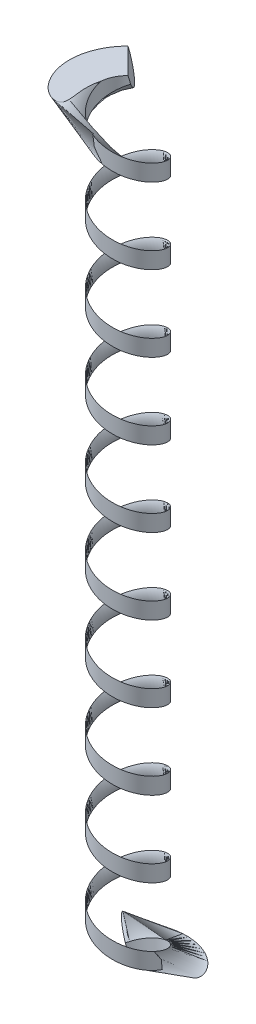
SolidWorks part; units mm, degrees
ref_plane "Front" through (0, 0, 0) normal (0, 0, 1) x (1, 0, 0)
ref_plane "Top" through (0, 0, 0) normal (0, 1, 0) x (1, 0, 0)
ref_plane "Right" through (0, 0, 0) normal (1, 0, 0) x (0, 0, -1)
sketch "Sketch1" plane through (0, 0, 0) normal (0, 1, 0) x (1, 0, 0)
  circle A0 centre (0, 0) radius 3.175
  point P4 (0, 0)
  dimension "D1" = 6.35
curve "Helix/Spiral1" pitch 5.08 height 50.8 turns 10
sweep "Sweep1" add path "Helix/Spiral1" circular profile diameter 2.54 parameters "D3"=2.54
sketch "Sketch10" plane through (0, 0, 0) normal (1, 0, 0) x (0, 0, -1)
  line L5 (-5.7814, 56.4483) -> (10.2716, 56.4483)
  line L6 (-5.7814, 56.4483) -> (-5.7814, 50.8)
  line L7 (-5.7814, 50.8) -> (10.2716, 50.8)
  line L8 (10.2716, 56.4483) -> (10.2716, 50.8)
  line L9 (-7.3012, 0) -> (8.8113, 0)
  line L10 (-7.3012, 0) -> (-7.3012, -4.697)
  line L11 (-7.3012, -4.697) -> (8.8113, -4.697)
  line L12 (8.8113, 0) -> (8.8113, -4.697)
  spline S0 degree 3 poles (2.2451, 0) (2.5372, 0.1052) (3.0105, 0.3178) (3.2574, 0.6349) (3.0097, 0.9525) (2.3035, 1.27) (1.2467, 1.5875) (0, 1.905) (-1.2467, 2.2225) (-2.3035, 2.54) (-3.0097, 2.8575) (-3.2577, 3.175) (-3.0097, 3.4925) (-2.3035, 3.81) (-0.8944, 4.2333) (0.8944, 4.6567) (2.3035, 5.08) (3.0097, 5.3975) (3.2577, 5.715) (3.0097, 6.0325) (2.3035, 6.35) (0.8944, 6.7733) (-0.8944, 7.1967) (-2.3035, 7.62) (-3.0097, 7.9375) (-3.2577, 8.255) (-3.0097, 8.5725) (-2.3035, 8.89) (-0.8944, 9.3133) (0.8944, 9.7367) (2.3035, 10.16) (3.0097, 10.4775) (3.2577, 10.795) (3.0097, 11.1125) (2.3035, 11.43) (0.8944, 11.8533) (-0.8944, 12.2767) (-2.3035, 12.7) (-3.0097, 13.0175) (-3.2577, 13.335) (-3.0097, 13.6525) (-2.3035, 13.97) (-0.8944, 14.3933) (0.8944, 14.8167) (2.3035, 15.24) (3.0097, 15.5575) (3.2577, 15.875) (3.0097, 16.1925) (2.3035, 16.51) (0.8944, 16.9333) (-0.8944, 17.3567) (-2.3035, 17.78) (-3.0097, 18.0975) (-3.2577, 18.415) (-3.0097, 18.7325) (-2.3035, 19.05) (-0.8944, 19.4733) (0.8944, 19.8967) (2.3035, 20.32) (3.0097, 20.6375) (3.2577, 20.955) (3.0097, 21.2725) (2.3035, 21.59) (0.8944, 22.0133) (-0.8944, 22.4367) (-2.3035, 22.86) (-3.0097, 23.1775) (-3.2577, 23.495) (-3.0097, 23.8125) (-2.3035, 24.13) (-0.8944, 24.5533) (0.8944, 24.9767) (2.3035, 25.4) (3.0097, 25.7175) (3.2577, 26.035) (3.0097, 26.3525) (2.3035, 26.67) (0.8944, 27.0933) (-0.8944, 27.5167) (-2.3035, 27.94) (-3.0097, 28.2575) (-3.2577, 28.575) (-3.0097, 28.8925) (-2.3035, 29.21) (-0.8944, 29.6333) (0.8944, 30.0567) (2.3035, 30.48) (3.0097, 30.7975) (3.2577, 31.115) (3.0097, 31.4325) (2.3035, 31.75) (0.8944, 32.1733) (-0.8944, 32.5967) (-2.3035, 33.02) (-3.0097, 33.3375) (-3.2577, 33.655) (-3.0097, 33.9725) (-2.3035, 34.29) (-0.8944, 34.7133) (0.8944, 35.1367) (2.3035, 35.56) (3.0097, 35.8775) (3.2577, 36.195) (3.0097, 36.5125) (2.3035, 36.83) (0.8944, 37.2533) (-0.8944, 37.6767) (-2.3035, 38.1) (-3.0097, 38.4175) (-3.2577, 38.735) (-3.0097, 39.0525) (-2.3035, 39.37) (-0.8944, 39.7933) (0.8944, 40.2167) (2.3035, 40.64) (3.0097, 40.9575) (3.2577, 41.275) (3.0097, 41.5925) (2.3035, 41.91) (0.8944, 42.3333) (-0.8944, 42.7567) (-2.3035, 43.18) (-3.0097, 43.4975) (-3.2577, 43.815) (-3.0097, 44.1325) (-2.3035, 44.45) (-0.8944, 44.8733) (0.8944, 45.2967) (2.3035, 45.72) (3.0097, 46.0375) (3.2577, 46.355) (3.0097, 46.6725) (2.3035, 46.99) (0.8944, 47.4133) (-0.8944, 47.8367) (-2.3035, 48.26) (-3.0097, 48.5775) (-3.2577, 48.895) (-3.0097, 49.2125) (-2.3035, 49.53) (-1.2467, 49.8475) (0.0002, 50.1651) (1.2458, 50.4822) (1.953, 50.6948) (2.2451, 50.8) knots 0 0 0 0 0.00625 0.0125 0.01875 0.025 0.03125 0.0375 0.04375 0.05 0.05625 0.0625 0.06875 0.075 0.08125 0.09375 0.1 0.10625 0.1125 0.11875 0.125 0.13125 0.14375 0.15 0.15625 0.1625 0.16875 0.175 0.18125 0.19375 0.2 0.20625 0.2125 0.21875 0.225 0.23125 0.24375 0.25 0.25625 0.2625 0.26875 0.275 0.28125 0.29375 0.3 0.30625 0.3125 0.31875 0.325 0.33125 0.34375 0.35 0.35625 0.3625 0.36875 0.375 0.38125 0.39375 0.4 0.40625 0.4125 0.41875 0.425 0.43125 0.44375 0.45 0.45625 0.4625 0.46875 0.475 0.48125 0.49375 0.5 0.50625 0.5125 0.51875 0.525 0.53125 0.54375 0.55 0.55625 0.5625 0.56875 0.575 0.58125 0.59375 0.6 0.60625 0.6125 0.61875 0.625 0.63125 0.64375 0.65 0.65625 0.6625 0.66875 0.675 0.68125 0.69375 0.7 0.70625 0.7125 0.71875 0.725 0.73125 0.74375 0.75 0.75625 0.7625 0.76875 0.775 0.78125 0.79375 0.8 0.80625 0.8125 0.81875 0.825 0.83125 0.84375 0.85 0.85625 0.8625 0.86875 0.875 0.88125 0.89375 0.9 0.90625 0.9125 0.91875 0.925 0.93125 0.94375 0.95 0.95625 0.9625 0.96875 0.975 0.98125 0.9875 0.99375 1 1 1 1 construction
  point P8 (2.2451, 50.8)
  point P9 (2.2451, 0)
  point P12 (2.2451, 50.8)
extrude "Cut-Extrude1" cut sketch "Sketch10" against normal through all both and the other way through all
sketch "Sketch13" plane through (0, 0, 0) normal (0, 1, 0) x (1, 0, 0)
  circle A0 centre (0, 0) radius 2.019
extrude "Cut-Extrude3" cut sketch "Sketch13" against normal through all both and the other way through all
